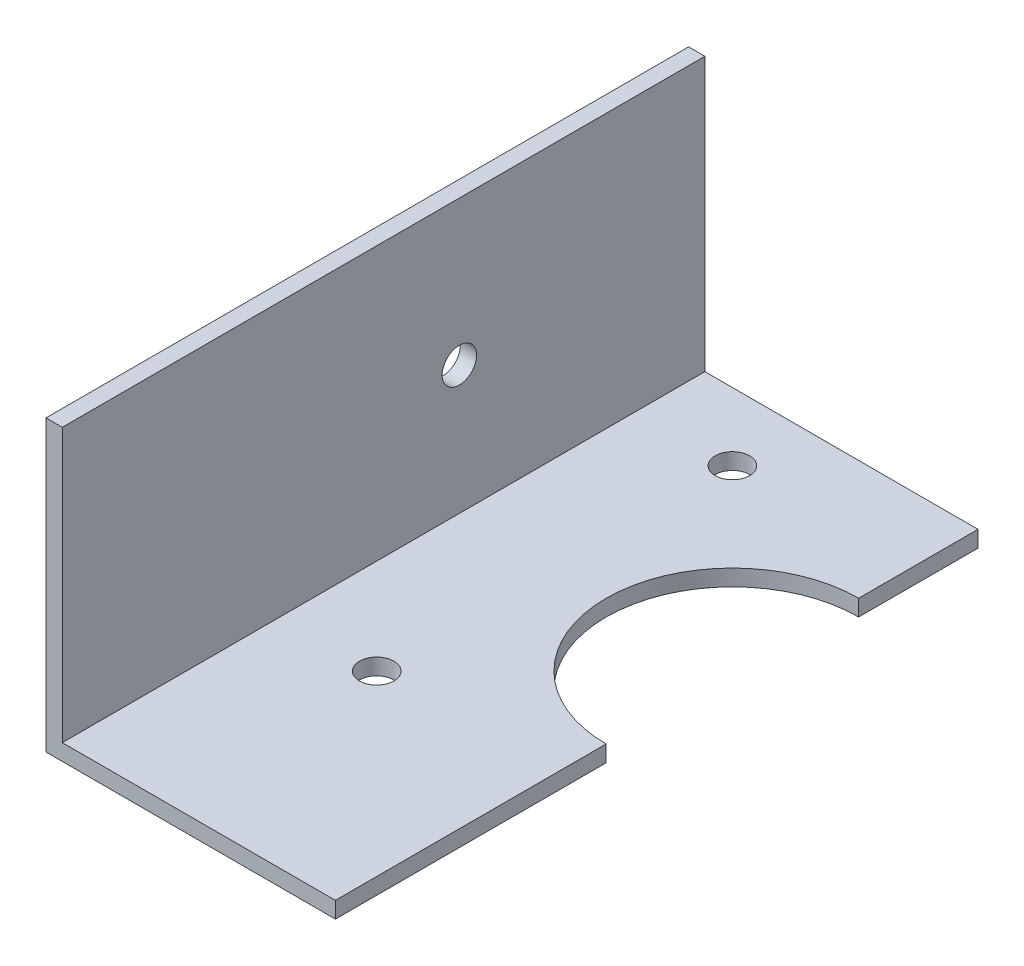
SolidWorks part; units mm, degrees
ref_plane "Front" through (0, 0, 0) normal (0, 0, 1) x (1, 0, 0)
ref_plane "Top" through (0, 0, 0) normal (0, 1, 0) x (1, 0, 0)
ref_plane "Right" through (0, 0, 0) normal (1, 0, 0) x (0, 0, -1)
sketch "Sketch1" plane through (0, 0, 0) normal (0, 0, 1) x (1, 0, 0)
  line L0 (0, 0) -> (0, -25.22)
  line L1 (25.22, -25.22) -> (0, -25.22)
  line L2 (25.22, -25.22) -> (25.22, -23.8)
  line L3 (25.22, -23.8) -> (1.42, -23.8)
  line L4 (1.42, 0) -> (1.42, -23.8)
  line L5 (1.42, 0) -> (0, 0)
extrude "Extrude1" add sketch "Sketch1" along normal blind 56
sketch "Sketch2" plane through (0, 0, 0) normal (-1, 0, 0) x (0, 0, 1)
  circle A0 centre (21.4, -12.61) radius 1.5
extrude "Cut-Extrude1" cut sketch "Sketch2" against normal through all
sketch "Sketch3" plane through (0, -25.22, 0) normal (0, -1, 0) x (1, 0, 0)
  line L0 (25.22, 56) -> (25.22, 0) construction
  circle A0 centre (25.22, 21.4) radius 11
extrude "Cut-Extrude2" cut sketch "Sketch3" against normal through all
sketch "Sketch4" plane through (0, -25.22, 0) normal (0, -1, 0) x (1, 0, 0)
  circle A0 centre (9.72, 36.9) radius 1.5
extrude "Cut-Extrude3" cut sketch "Sketch4" against normal through all
sketch "Sketch5" plane through (0, -25.22, 0) normal (0, -1, 0) x (1, 0, 0)
  circle A0 centre (9.72, 5.9) radius 1.5
extrude "Cut-Extrude4" cut sketch "Sketch5" against normal through all
